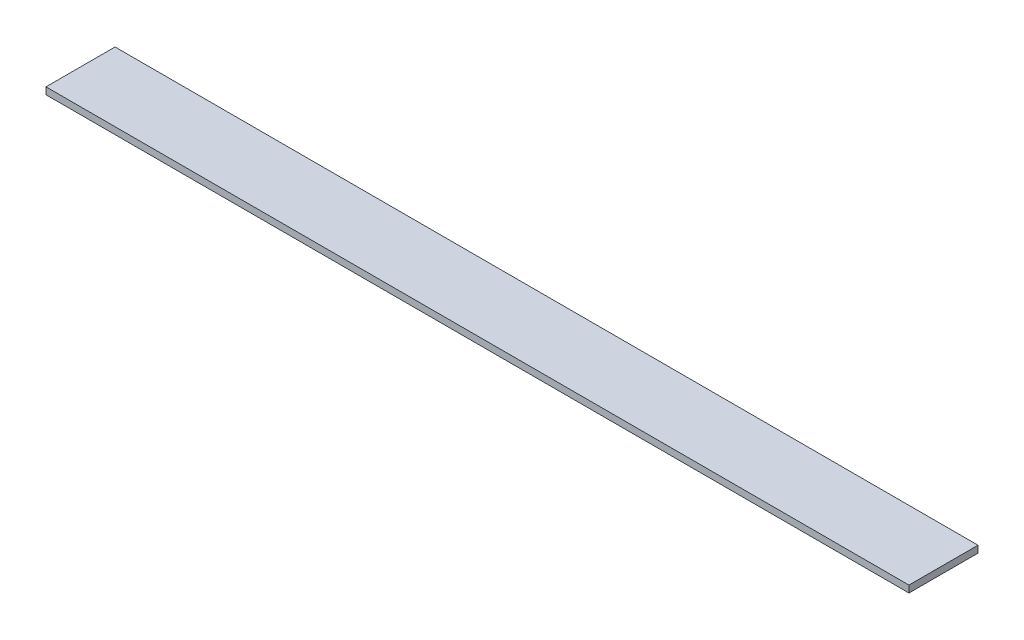
SolidWorks part; units mm, degrees
ref_plane "Front Plane" through (0, 0, 0) normal (0, 0, 1) x (1, 0, 0)
ref_plane "Top Plane" through (0, 0, 0) normal (0, 1, 0) x (1, 0, 0)
ref_plane "Right Plane" through (0, 0, 0) normal (1, 0, 0) x (0, 0, -1)
sketch "Sketch1" plane through (0, 0, 0) normal (0, 1, 0) x (1, 0, 0)
  line L0 (-625, 50) -> (625, -50) construction
  line L1 (-625, 50) -> (625, 50)
  line L2 (-625, 50) -> (-625, -50)
  line L3 (-625, -50) -> (625, -50)
  line L4 (625, 50) -> (625, -50)
  dimension "D1" = 1250
  dimension "D2" = 100
extrude "Boss-Extrude1" add sketch "Sketch1" along normal blind 10
